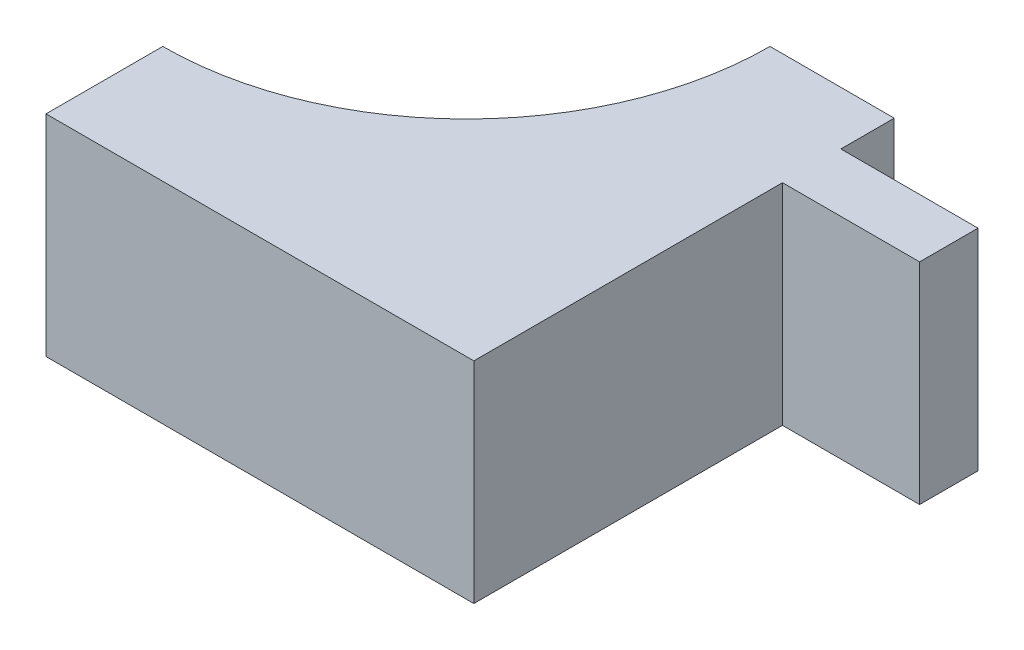
SolidWorks part; units mm, degrees
ref_plane "Front Plane" through (0, 0, 0) normal (0, 0, 1) x (1, 0, 0)
ref_plane "Top Plane" through (0, 0, 0) normal (0, 1, 0) x (1, 0, 0)
ref_plane "Right Plane" through (0, 0, 0) normal (1, 0, 0) x (0, 0, -1)
sketch "Sketch1" plane through (0, 0, 0) normal (0, 1, 0) x (1, 0, 0)
  line L3 (-24, 305) -> (-13.36, 305)
  line L5 (-50, 279) -> (-50, 269)
  line L6 (-50, 269) -> (-13.36, 269)
  line L14 (-13.36, 269) -> (-13.36, 295.43)
  line L15 (-13.36, 300.43) -> (-1.6161, 300.43)
  line L16 (-1.6161, 300.43) -> (-1.6161, 295.43)
  line L17 (-1.6161, 295.43) -> (-13.36, 295.43)
  line L19 (-13.36, 300.43) -> (-13.36, 305)
  arc A1 (-50, 279) -> (-24, 305) centre (-50, 305) ccw
  dimension "D1" = 26
  dimension "D2" = 4.57
  dimension "D3" = 5
  dimension "D4" = 36.64
  dimension "D6" = 36
extrude "Boss-Extrude1" add sketch "Sketch1" along normal blind 18
